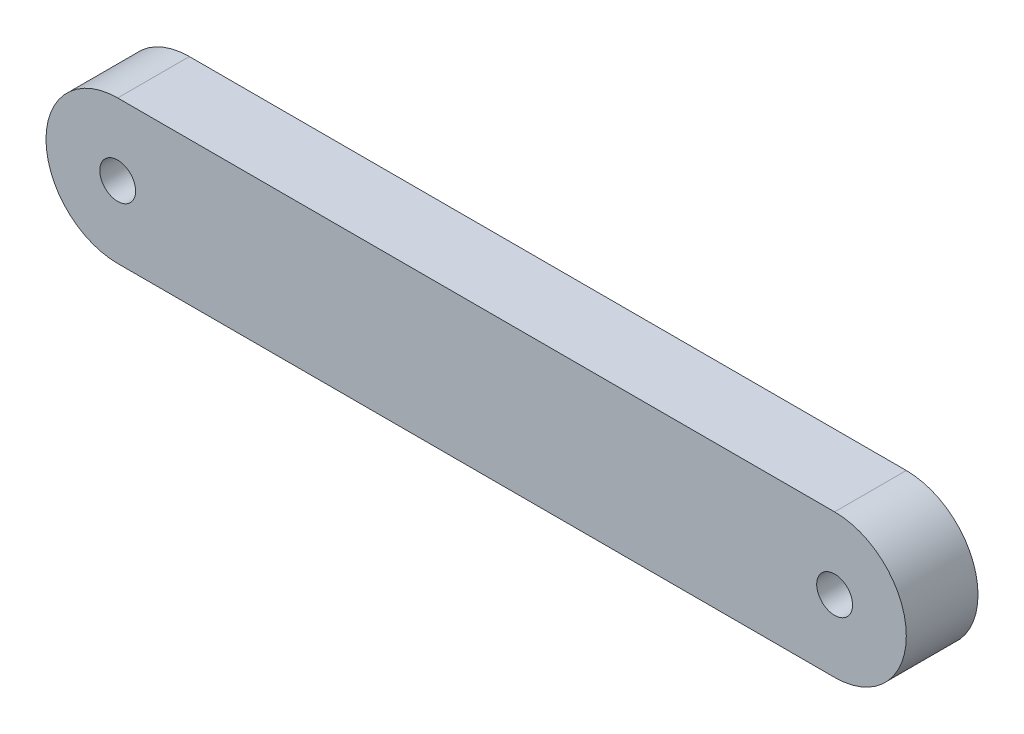
SolidWorks part; units mm, degrees
ref_plane "Front Plane" through (0, 0, 0) normal (0, 0, 1) x (1, 0, 0)
ref_plane "Top Plane" through (0, 0, 0) normal (0, 1, 0) x (1, 0, 0)
ref_plane "Right Plane" through (0, 0, 0) normal (1, 0, 0) x (0, 0, -1)
sketch "Sketch1" plane through (0, 0, 0) normal (0, 0, 1) x (1, 0, 0)
  line L0 (0, 0) -> (25.4, 0) construction
  line L1 (0, 2.54) -> (25.4, 2.54)
  line L2 (0, -2.54) -> (25.4, -2.54)
  arc A0 (0, 2.54) -> (0, -2.54) centre (0, 0) ccw
  arc A1 (25.4, -2.54) -> (25.4, 2.54) centre (25.4, 0) ccw
  point P3 (12.7, 0)
  dimension "D1" = 2.54
  dimension "D2" = 25.4
extrude "Boss-Extrude1" add sketch "Sketch1" along normal blind 2.54
sketch "Sketch2" plane through (0, 0, 2.54) normal (0, 0, 1) x (1, 0, 0)
  circle A0 centre (0, 0) radius 0.635
  dimension "D1" = 1.27
extrude "Cut-Extrude1" cut sketch "Sketch2" against normal through all both and the other way through all
ref_plane "Plane1" through (12.7, 0, 0) normal (1, 0, 0) x (0, 0, -1)
mirror "Mirror1" about plane through (12.7, 0, 0) normal (1, 0, 0) of "Cut-Extrude1"
